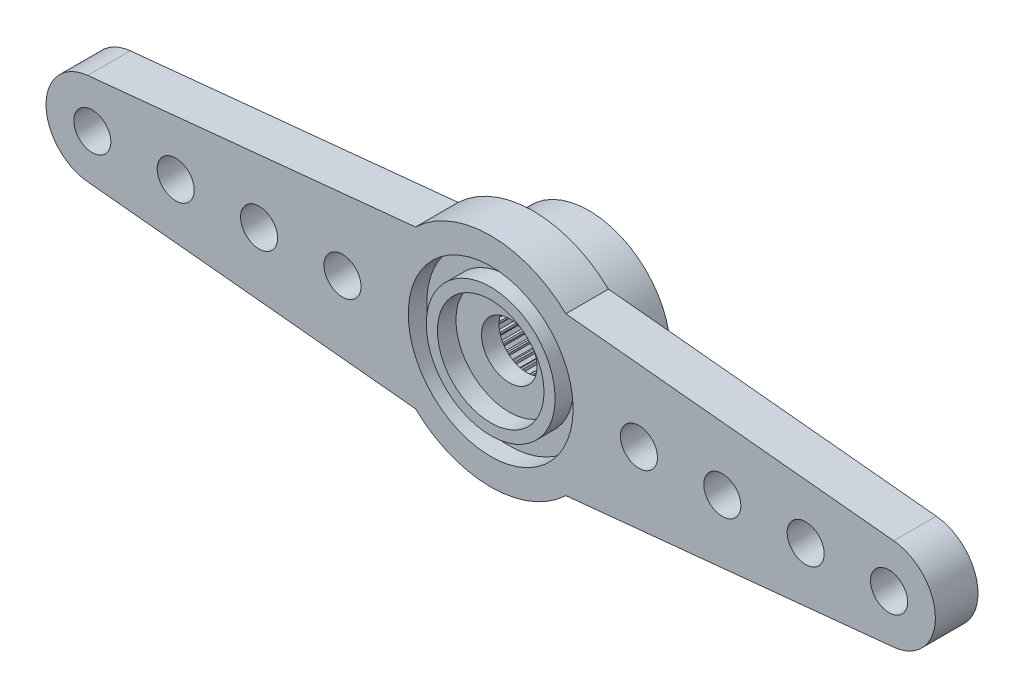
SolidWorks part; units mm, degrees
ref_plane "Plan de face" through (0, 0, 0) normal (0, 0, 1) x (1, 0, 0)
ref_plane "Plan de dessus" through (0, 0, 0) normal (0, 1, 0) x (1, 0, 0)
ref_plane "Plan de droite" through (0, 0, 0) normal (1, 0, 0) x (0, 0, -1)
sketch "Esquisse1" plane through (0, 0, 0) normal (0, 0, 1) x (1, 0, 0)
  line L0 (-21.5, 0) -> (0, 0) construction
  line L1 (-4.0562, 4.25) -> (-4.0562, -4.25) construction
  line L2 (-21.7478, 2.4877) -> (-4.0562, 4.25)
  line L3 (-21.7478, -2.4877) -> (-4.0562, -4.25)
  line L4 (0, 0) -> (0, 5.875) construction
  line L5 (21.7478, -2.4877) -> (4.0562, -4.25)
  line L6 (21.7478, 2.4877) -> (4.0562, 4.25)
  arc A0 (-4.0562, -4.25) -> (4.0562, -4.25) centre (0, 0) ccw
  arc A3 (-21.7478, 2.4877) -> (-21.7478, -2.4877) centre (-21.5, 0) ccw
  arc A4 (21.7478, 2.4877) -> (21.7478, -2.4877) centre (21.5, 0) cw
  arc A5 (4.0562, 4.25) -> (-4.0562, 4.25) centre (0, 0) ccw
  dimension "D1" = 11.75
  dimension "D2" = 2.5
  dimension "D3" = 43
  dimension "D5" = 8.5
extrude "Boss.-Extru.1" add sketch "Esquisse1" along normal blind 2.3
sketch "Esquisse2" plane through (0, 0, 2.3) normal (0, 0, 1) x (1, 0, 0)
  circle A0 centre (0, 0) radius 4.45
  dimension "D1" = 8.9
extrude "Enlèv. mat.-Extru.1" cut sketch "Esquisse2" against normal blind 1
sketch "Esquisse3" plane through (0, 0, 1.3) normal (0, 0, 1) x (1, 0, 0)
  circle A0 centre (0, 0) radius 2.875
  circle A1 centre (0, 0) radius 3.475
  dimension "D1" = 5.75
  dimension "D2" = 0.6
extrude "Boss.-Extru.2" add sketch "Esquisse3" along normal up to surface (1 mm away) up to face at (4.45, 0, 2.3)
sketch "Esquisse4" plane through (0, 0, 0) normal (0, 0, -1) x (-1, 0, 0)
  circle A0 centre (0, 0) radius 4.4
  dimension "D1" = 8.8
extrude "Boss.-Extru.3" add sketch "Esquisse4" along normal blind 3
sketch "Esquisse5" plane through (0, 0, 1.3) normal (0, 0, 1) x (1, 0, 0)
  circle A0 centre (0, 0) radius 1.5
  dimension "D1" = 3
extrude "Enlèv. mat.-Extru.2" cut sketch "Esquisse5" against normal through all
sketch "Esquisse6" plane through (0, 0, -3) normal (0, 0, -1) x (-1, 0, 0)
  line L0 (-0.1143, 2.9978) -> (-0.0406, 2.8652)
  line L1 (0.0406, 2.8652) -> (0.1143, 2.9978)
  line L2 (0, 2.8652) -> (0, 0) construction
  line L3 (-0.0406, 2.8652) -> (0.0406, 2.8652)
  line L4 (0.439, 2.8316) -> (0.5304, 2.9527)
  line L5 (0.3041, 2.9846) -> (0.3585, 2.8429)
  line L6 (0.3585, 2.8429) -> (0.439, 2.8316)
  line L7 (0.8288, 2.743) -> (0.9362, 2.8502)
  line L8 (0.7165, 2.9132) -> (0.7507, 2.7654)
  line L9 (0.7507, 2.7654) -> (0.8288, 2.743)
  line L10 (1.2025, 2.6009) -> (1.3237, 2.6922)
  line L11 (1.1149, 2.7851) -> (1.1283, 2.634)
  line L12 (1.1283, 2.634) -> (1.2025, 2.6009)
  line L13 (1.5527, 2.4083) -> (1.6855, 2.4817)
  line L14 (1.4917, 2.6029) -> (1.4839, 2.4513)
  line L15 (1.4839, 2.4513) -> (1.5527, 2.4083)
  line L16 (1.8728, 2.1687) -> (2.0145, 2.223)
  line L17 (1.8394, 2.3699) -> (1.8106, 2.2209)
  line L18 (1.8106, 2.2209) -> (1.8728, 2.1687)
  line L19 (2.1564, 1.887) -> (2.3043, 1.921)
  line L20 (2.1514, 2.0909) -> (2.1021, 1.9473)
  line L21 (2.1021, 1.9473) -> (2.1564, 1.887)
  line L22 (2.398, 1.5685) -> (2.5492, 1.5816)
  line L23 (2.4214, 1.7711) -> (2.3526, 1.6358)
  line L24 (2.3526, 1.6358) -> (2.398, 1.5685)
  line L25 (2.593, 1.2195) -> (2.7445, 1.2114)
  line L26 (2.6443, 1.4169) -> (2.5574, 1.2925)
  line L27 (2.5574, 1.2925) -> (2.593, 1.2195)
  line L28 (2.7375, 0.8468) -> (2.8864, 0.8177)
  line L29 (2.8158, 1.0351) -> (2.7124, 0.924)
  line L30 (2.7124, 0.924) -> (2.7375, 0.8468)
  line L31 (2.8287, 0.4575) -> (2.9721, 0.408)
  line L32 (2.9324, 0.6331) -> (2.8146, 0.5375)
  line L33 (2.8146, 0.5375) -> (2.8287, 0.4575)
  line L34 (2.8648, 0.0594) -> (3, -0.0096)
  line L35 (2.992, 0.2188) -> (2.862, 0.1406)
  line L36 (2.862, 0.1406) -> (2.8648, 0.0594)
  line L37 (2.8452, -0.3399) -> (2.9695, -0.427)
  line L38 (2.9933, -0.1997) -> (2.8537, -0.2591)
  line L39 (2.8537, -0.2591) -> (2.8452, -0.3399)
  line L40 (2.7702, -0.7325) -> (2.8811, -0.8361)
  line L41 (2.9364, -0.6144) -> (2.7899, -0.6537)
  line L42 (2.7899, -0.6537) -> (2.7702, -0.7325)
  line L43 (2.6413, -1.111) -> (2.7367, -1.229)
  line L44 (2.8223, -1.017) -> (2.6717, -1.0357)
  line L45 (2.6717, -1.0357) -> (2.6413, -1.111)
  line L46 (2.461, -1.4677) -> (2.5391, -1.5979)
  line L47 (2.6533, -1.3999) -> (2.5016, -1.3974)
  line L48 (2.5016, -1.3974) -> (2.461, -1.4677)
  line L49 (2.2328, -1.796) -> (2.292, -1.9357)
  line L50 (2.4327, -1.7556) -> (2.2828, -1.732)
  line L51 (2.2828, -1.732) -> (2.2328, -1.796)
  line L52 (1.9611, -2.0892) -> (2.0003, -2.2358)
  line L53 (2.1647, -2.0771) -> (2.0195, -2.0328)
  line L54 (2.0195, -2.0328) -> (1.9611, -2.0892)
  line L55 (1.6512, -2.3418) -> (1.6696, -2.4925)
  line L56 (1.8545, -2.3581) -> (1.7169, -2.2941)
  line L57 (1.7169, -2.2941) -> (1.6512, -2.3418)
  line L58 (1.3093, -2.5488) -> (1.3065, -2.7006)
  line L59 (1.5083, -2.5933) -> (1.381, -2.5107)
  line L60 (1.381, -2.5107) -> (1.3093, -2.5488)
  line L61 (0.9418, -2.7063) -> (0.9179, -2.8561)
  line L62 (1.1327, -2.7779) -> (1.0181, -2.6785)
  line L63 (1.0181, -2.6785) -> (0.9418, -2.7063)
  line L64 (0.556, -2.811) -> (0.5115, -2.9561)
  line L65 (0.7351, -2.9086) -> (0.6354, -2.7941)
  line L66 (0.6354, -2.7941) -> (0.556, -2.811)
  line L67 (0.1594, -2.861) -> (0.0951, -2.9985)
  line L68 (0.3231, -2.9825) -> (0.2404, -2.8553)
  line L69 (0.2404, -2.8553) -> (0.1594, -2.861)
  line L70 (-0.2404, -2.8553) -> (-0.3231, -2.9825)
  line L71 (-0.0951, -2.9985) -> (-0.1594, -2.861)
  line L72 (-0.1594, -2.861) -> (-0.2404, -2.8553)
  line L73 (-0.6354, -2.7941) -> (-0.7351, -2.9086)
  line L74 (-0.5115, -2.9561) -> (-0.556, -2.811)
  line L75 (-0.556, -2.811) -> (-0.6354, -2.7941)
  line L76 (-1.0181, -2.6785) -> (-1.1327, -2.7779)
  line L77 (-0.9179, -2.8561) -> (-0.9418, -2.7063)
  line L78 (-0.9418, -2.7063) -> (-1.0181, -2.6785)
  line L79 (-1.381, -2.5107) -> (-1.5083, -2.5933)
  line L80 (-1.3065, -2.7006) -> (-1.3093, -2.5488)
  line L81 (-1.3093, -2.5488) -> (-1.381, -2.5107)
  line L82 (-1.7169, -2.2941) -> (-1.8545, -2.3581)
  line L83 (-1.6696, -2.4925) -> (-1.6512, -2.3418)
  line L84 (-1.6512, -2.3418) -> (-1.7169, -2.2941)
  line L85 (-2.0195, -2.0328) -> (-2.1647, -2.0771)
  line L86 (-2.0003, -2.2358) -> (-1.9611, -2.0892)
  line L87 (-1.9611, -2.0892) -> (-2.0195, -2.0328)
  line L88 (-2.2828, -1.732) -> (-2.4327, -1.7556)
  line L89 (-2.292, -1.9357) -> (-2.2328, -1.796)
  line L90 (-2.2328, -1.796) -> (-2.2828, -1.732)
  line L91 (-2.5016, -1.3974) -> (-2.6533, -1.3999)
  line L92 (-2.5391, -1.5979) -> (-2.461, -1.4677)
  line L93 (-2.461, -1.4677) -> (-2.5016, -1.3974)
  line L94 (-2.6717, -1.0357) -> (-2.8223, -1.017)
  line L95 (-2.7367, -1.229) -> (-2.6413, -1.111)
  line L96 (-2.6413, -1.111) -> (-2.6717, -1.0357)
  line L97 (-2.7899, -0.6537) -> (-2.9364, -0.6144)
  line L98 (-2.8811, -0.8361) -> (-2.7702, -0.7325)
  line L99 (-2.7702, -0.7325) -> (-2.7899, -0.6537)
  line L100 (-2.8537, -0.2591) -> (-2.9933, -0.1997)
  line L101 (-2.9695, -0.427) -> (-2.8452, -0.3399)
  line L102 (-2.8452, -0.3399) -> (-2.8537, -0.2591)
  line L103 (-2.862, 0.1406) -> (-2.992, 0.2188)
  line L104 (-3, -0.0096) -> (-2.8648, 0.0594)
  line L105 (-2.8648, 0.0594) -> (-2.862, 0.1406)
  line L106 (-2.8146, 0.5375) -> (-2.9324, 0.6331)
  line L107 (-2.9721, 0.408) -> (-2.8287, 0.4575)
  line L108 (-2.8287, 0.4575) -> (-2.8146, 0.5375)
  line L109 (-2.7124, 0.924) -> (-2.8158, 1.0351)
  line L110 (-2.8864, 0.8177) -> (-2.7375, 0.8468)
  line L111 (-2.7375, 0.8468) -> (-2.7124, 0.924)
  line L112 (-2.5574, 1.2925) -> (-2.6443, 1.4169)
  line L113 (-2.7445, 1.2114) -> (-2.593, 1.2195)
  line L114 (-2.593, 1.2195) -> (-2.5574, 1.2925)
  line L115 (-2.3526, 1.6358) -> (-2.4214, 1.7711)
  line L116 (-2.5492, 1.5816) -> (-2.398, 1.5685)
  line L117 (-2.398, 1.5685) -> (-2.3526, 1.6358)
  line L118 (-2.1021, 1.9473) -> (-2.1514, 2.0909)
  line L119 (-2.3043, 1.921) -> (-2.1564, 1.887)
  line L120 (-2.1564, 1.887) -> (-2.1021, 1.9473)
  line L121 (-1.8106, 2.2209) -> (-1.8394, 2.3699)
  line L122 (-2.0145, 2.223) -> (-1.8728, 2.1687)
  line L123 (-1.8728, 2.1687) -> (-1.8106, 2.2209)
  line L124 (-1.4839, 2.4513) -> (-1.4917, 2.6029)
  line L125 (-1.6855, 2.4817) -> (-1.5527, 2.4083)
  line L126 (-1.5527, 2.4083) -> (-1.4839, 2.4513)
  line L127 (-1.1283, 2.634) -> (-1.1149, 2.7851)
  line L128 (-1.3237, 2.6922) -> (-1.2025, 2.6009)
  line L129 (-1.2025, 2.6009) -> (-1.1283, 2.634)
  line L130 (-0.7507, 2.7654) -> (-0.7165, 2.9132)
  line L131 (-0.9362, 2.8502) -> (-0.8288, 2.743)
  line L132 (-0.8288, 2.743) -> (-0.7507, 2.7654)
  line L133 (-0.3585, 2.8429) -> (-0.3041, 2.9846)
  line L134 (-0.5304, 2.9527) -> (-0.439, 2.8316)
  line L135 (-0.439, 2.8316) -> (-0.3585, 2.8429)
  circle A0 centre (0, 0) radius 3
  point P187 (0, 0)
  dimension "D1" = 6
  dimension "D2" = 45
extrude "Enlèv. mat.-Extru.3" cut sketch "Esquisse6" against normal blind 3.35
sketch "Esquisse7" plane through (0, 0, 2.3) normal (0, 0, 1) x (1, 0, 0)
  line L2 (0, -2.915) -> (0, 2.915) construction
  circle A0 centre (-21.5, 0) radius 1
  circle A7 centre (-17, 0) radius 1
  circle A8 centre (-12.5, 0) radius 1
  circle A9 centre (-8, 0) radius 1
  circle A10 centre (8, 0) radius 1
  circle A11 centre (12.5, 0) radius 1
  circle A12 centre (17, 0) radius 1
  circle A13 centre (21.5, 0) radius 1
  dimension "D1" = 2
  dimension "D2" = 4
extrude "Enlèv. mat.-Extru.4" cut sketch "Esquisse7" against normal blind 3.35
sketch "Sketch1" plane through (0, 0, 2.3) normal (0, 0, 1) x (1, 0, 0)
  line L0 (3.9348, 4.3627) -> (25.8463, 4.6561)
  line L1 (25.8463, 4.6561) -> (25.8463, -3.3922)
  line L2 (25.8463, -3.3922) -> (3.5705, -4.6655)
  arc A0 (4.0562, 4.25) -> (-4.0562, 4.25) centre (0, 0) ccw construction
  arc A1 (-4.0562, -4.25) -> (4.0562, -4.25) centre (0, 0) ccw construction
  arc A2 (3.5705, -4.6655) -> (3.9348, 4.3627) centre (0, 0) ccw
  dimension "D1" = 21.9115
  dimension "D2" = 8.0483
  dimension "D3" = 22.2758
extrude "Cut-Extrude1" [suppressed] cut sketch "Sketch1" against normal blind 10
scale "Scale1" [suppressed]
scale "Scale2" scale about centroid uniform scaling yes scale factor 0.833333
